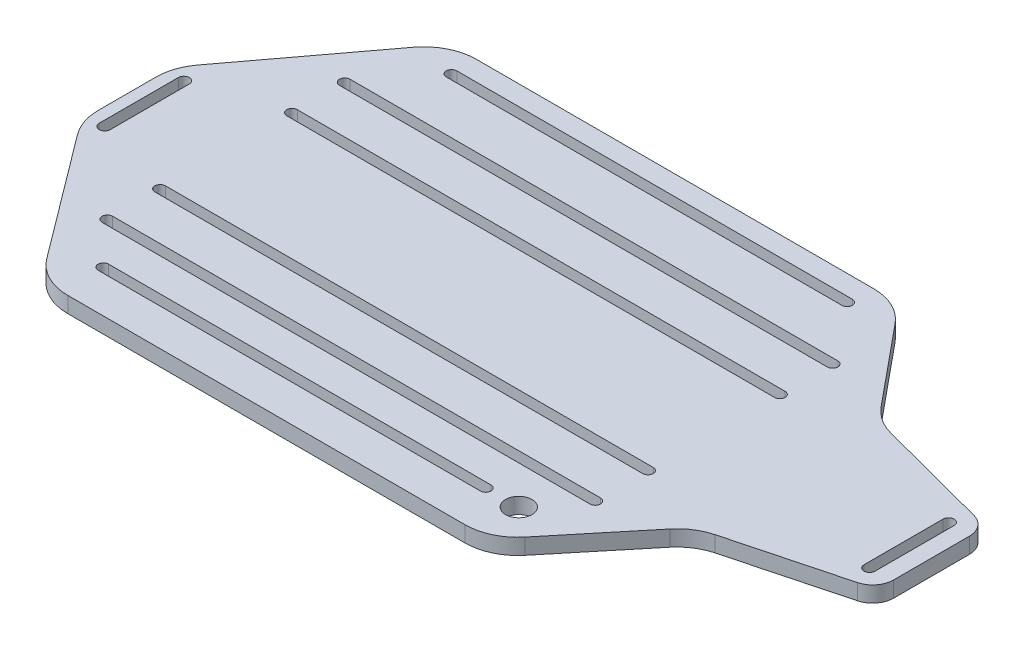
SolidWorks part; units mm, degrees
ref_plane "Front Plane" through (0, 0, 0) normal (0, 0, 1) x (1, 0, 0)
ref_plane "Top Plane" through (0, 0, 0) normal (0, 1, 0) x (1, 0, 0)
ref_plane "Right Plane" through (0, 0, 0) normal (1, 0, 0) x (0, 0, -1)
sketch "Sketch1" plane through (0, 0, 0) normal (0, 1, 0) x (1, 0, 0)
  line L0 (-91, -69.5) -> (-126, -22.8333)
  line L1 (75.5615, -77.5) -> (-75, -77.5)
  line L2 (85, -77.5) -> (85, 77.5) construction
  line L3 (75.5615, 77.5) -> (-75, 77.5)
  line L4 (-85, -77.5) -> (-85, 77.5) construction
  line L5 (85, -77.5) -> (-85, 77.5) construction
  line L6 (85, 77.5) -> (-85, -77.5) construction
  line L7 (-130, -10.8333) -> (-130, 10.8333)
  line L8 (-126, 22.8333) -> (-91, 69.5)
  line L9 (91.0001, 70.2141) -> (115.8985, 39.9803)
  line L10 (126.2386, 33.3553) -> (169.0394, 22.0714)
  line L11 (175, 14.3357) -> (175, -14.3357)
  line L12 (169.0394, -22.0714) -> (126.2386, -33.3553)
  line L13 (115.8985, -39.9803) -> (91.0001, -70.2141)
  line L14 (120, 35) -> (120, -35) construction
  arc A0 (126.2386, -33.3553) -> (115.8985, -39.9803) centre (131.3372, -52.6945) ccw
  arc A1 (126.2386, 33.3553) -> (115.8985, 39.9803) centre (131.3372, 52.6945) cw
  arc A2 (91.0001, 70.2141) -> (75.5615, 77.5) centre (75.5615, 57.5) ccw
  arc A3 (91.0001, -70.2141) -> (75.5615, -77.5) centre (75.5615, -57.5) cw
  arc A4 (-75, -77.5) -> (-91, -69.5) centre (-75, -57.5) cw
  arc A5 (-75, 77.5) -> (-91, 69.5) centre (-75, 57.5) ccw
  arc A6 (-126, 22.8333) -> (-130, 10.8333) centre (-110, 10.8333) ccw
  arc A7 (-130, -10.8333) -> (-126, -22.8333) centre (-110, -10.8333) ccw
  arc A8 (175, -14.3357) -> (169.0394, -22.0714) centre (167, -14.3357) cw
  arc A9 (175, 14.3357) -> (169.0394, 22.0714) centre (167, 14.3357) ccw
  point P0 (0, 0)
  point P32 (-130, 17.5)
  point P35 (-130, -17.5)
  point P38 (175, -20.5)
  point P41 (175, 20.5)
  dimension "D9" = 20
  dimension "D10" = 20
  dimension "D11" = 8
  dimension "D1" = 155
  dimension "D2" = 170
  dimension "D3" = 35
  dimension "D4" = 41
  dimension "D5" = 70
  dimension "D6" = 305
  dimension "D7" = 90
  dimension "D8" = 55
extrude "Boss-Extrude2" add sketch "Sketch1" along normal blind 6
sketch "Sketch2" plane through (0, 6, 0) normal (0, 1, 0) x (1, 0, 0)
  line L0 (166.5, 15) -> (166.5, -15) construction
  line L1 (168.6, 15) -> (168.6, -15)
  line L2 (164.4, 15) -> (164.4, -15)
  line L3 (-123.5, 15) -> (-123.5, -15) construction
  line L4 (-121.4, 15) -> (-121.4, -15)
  line L5 (-125.6, 15) -> (-125.6, -15)
  line L7 (-123.5, 0) -> (166.5, 0) construction
  line L8 (175, -14.3357) -> (175, 14.3357) construction
  line L9 (-75, -77.5) -> (75.5615, -77.5) construction
  line L10 (-92.5, 45) -> (92.5, 45) construction
  line L11 (-92.5, 47) -> (92.5, 47)
  line L12 (-92.5, 43) -> (92.5, 43)
  line L13 (-92.5, -45) -> (92.5, -45) construction
  line L14 (-92.5, -43) -> (92.5, -43)
  line L15 (-92.5, -47) -> (92.5, -47)
  line L16 (-92.5, 25) -> (92.5, 25) construction
  line L17 (-92.5, 27) -> (92.5, 27)
  line L18 (-92.5, 23) -> (92.5, 23)
  line L19 (-92.5, -25) -> (92.5, -25) construction
  line L20 (-92.5, -23) -> (92.5, -23)
  line L21 (-92.5, -27) -> (92.5, -27)
  line L22 (0, 45) -> (0, 25) construction
  line L23 (0, 0) -> (0, 25) construction
  line L24 (0, -25) -> (0, -45) construction
  line L25 (0, 0) -> (0, -25) construction
  line L26 (-75, 68) -> (75, 68) construction
  line L27 (-75, 70) -> (75, 70)
  line L28 (-75, 66) -> (75, 66)
  line L29 (-77.5373, -61.5) -> (67.4627, -61.5) construction
  line L30 (-77.5373, -59.5) -> (67.4627, -59.5)
  line L31 (-77.5373, -63.5) -> (67.4627, -63.5)
  line L32 (0, 45) -> (0, 68) construction
  line L33 (0, -45) -> (0, -61.5) construction
  arc A0 (168.6, 15) -> (164.4, 15) centre (166.5, 15) ccw
  arc A1 (164.4, -15) -> (168.6, -15) centre (166.5, -15) ccw
  arc A2 (-121.4, 15) -> (-125.6, 15) centre (-123.5, 15) ccw
  arc A3 (-125.6, -15) -> (-121.4, -15) centre (-123.5, -15) ccw
  circle A4 centre (80, -61.5) radius 5
  arc A5 (-92.5, 47) -> (-92.5, 43) centre (-92.5, 45) ccw
  arc A6 (92.5, 43) -> (92.5, 47) centre (92.5, 45) ccw
  arc A7 (-92.5, -43) -> (-92.5, -47) centre (-92.5, -45) ccw
  arc A8 (92.5, -47) -> (92.5, -43) centre (92.5, -45) ccw
  arc A9 (-92.5, 27) -> (-92.5, 23) centre (-92.5, 25) ccw
  arc A10 (92.5, 23) -> (92.5, 27) centre (92.5, 25) ccw
  arc A11 (-92.5, -23) -> (-92.5, -27) centre (-92.5, -25) ccw
  arc A12 (92.5, -27) -> (92.5, -23) centre (92.5, -25) ccw
  arc A13 (-75, 70) -> (-75, 66) centre (-75, 68) ccw
  arc A14 (75, 66) -> (75, 70) centre (75, 68) ccw
  arc A15 (-77.5373, -59.5) -> (-77.5373, -63.5) centre (-77.5373, -61.5) ccw
  arc A16 (67.4627, -63.5) -> (67.4627, -59.5) centre (67.4627, -61.5) ccw
  point P2 (166.5, 0)
  point P7 (-123.5, 0)
  point P25 (0, 45)
  point P30 (0, -45)
  point P39 (0, 25)
  point P44 (0, -25)
  point P51 (0, 68)
  point P63 (-5.0373, -61.5)
  point P70 (0.2808, -61.5)
  dimension "D1" = 8.5
  dimension "D4" = 10
  dimension "D7" = 2.1
  dimension "D8" = 2
  dimension "D11" = 185
  dimension "D2" = 30
  dimension "D3" = 290
  dimension "D5" = 95
  dimension "D6" = 16
  dimension "D9" = 25
  dimension "D10" = 20
  dimension "D12" = 23
  dimension "D13" = 150
  dimension "D14" = 145
extrude "Cut-Extrude2" cut sketch "Sketch2" against normal blind 6
